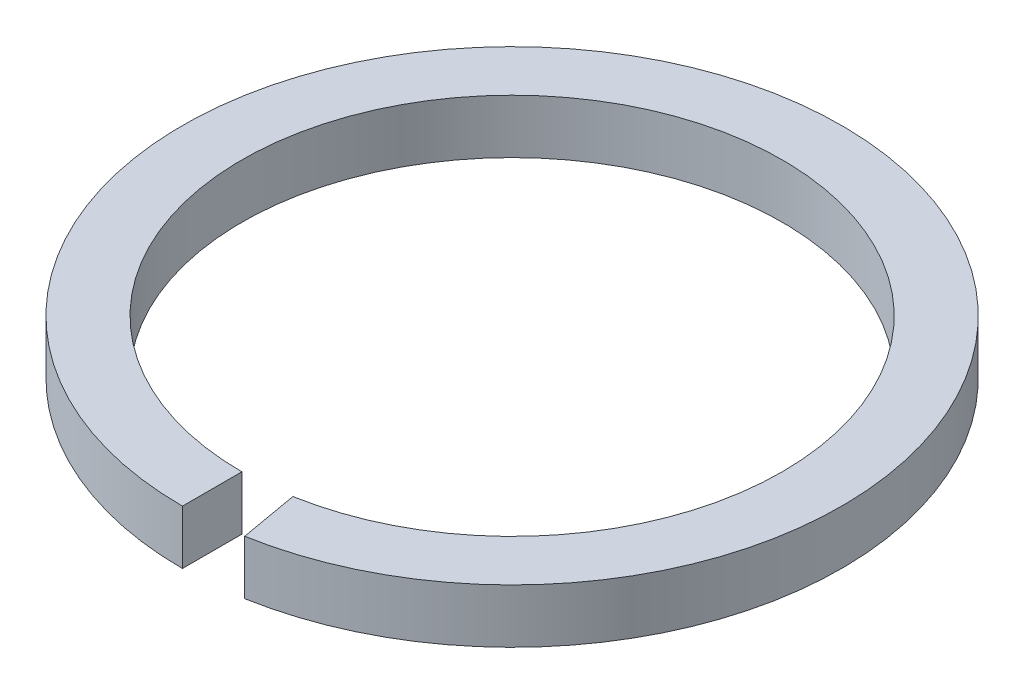
SolidWorks part; units mm, degrees
ref_plane "Front Plane" through (0, 0, 0) normal (0, 0, 1) x (1, 0, 0)
ref_plane "Top Plane" through (0, 0, 0) normal (0, 1, 0) x (1, 0, 0)
ref_plane "Right Plane" through (0, 0, 0) normal (1, 0, 0) x (0, 0, -1)
sketch "Sketch1" plane through (0, 0, 0) normal (0, 1, 0) x (1, 0, 0)
  circle A0 centre (0, 0) radius 12.5
  circle A1 centre (0, 0) radius 15.25
  dimension "D1" = 30.5
  dimension "D2" = 25
extrude "Extrude1" add sketch "Sketch1" along normal blind 2.5
sketch "Sketch2" plane through (0, 2.5, 0) normal (0, 1, 0) x (1, 0, 0)
  line L0 (0, -12.5) -> (0, -15.25)
  line L1 (2.1706, -12.3101) -> (2.6481, -15.0183)
  circle A0 centre (0, 0) radius 12.5 construction
  arc A1 (0, -12.5) -> (2.1706, -12.3101) centre (0, 0) ccw
  circle A2 centre (0, 0) radius 15.25 construction
  arc A3 (0, -15.25) -> (2.6481, -15.0183) centre (0, 0) ccw
  dimension "D1" = 10
extrude "Extrude2" cut sketch "Sketch2" against normal through all
